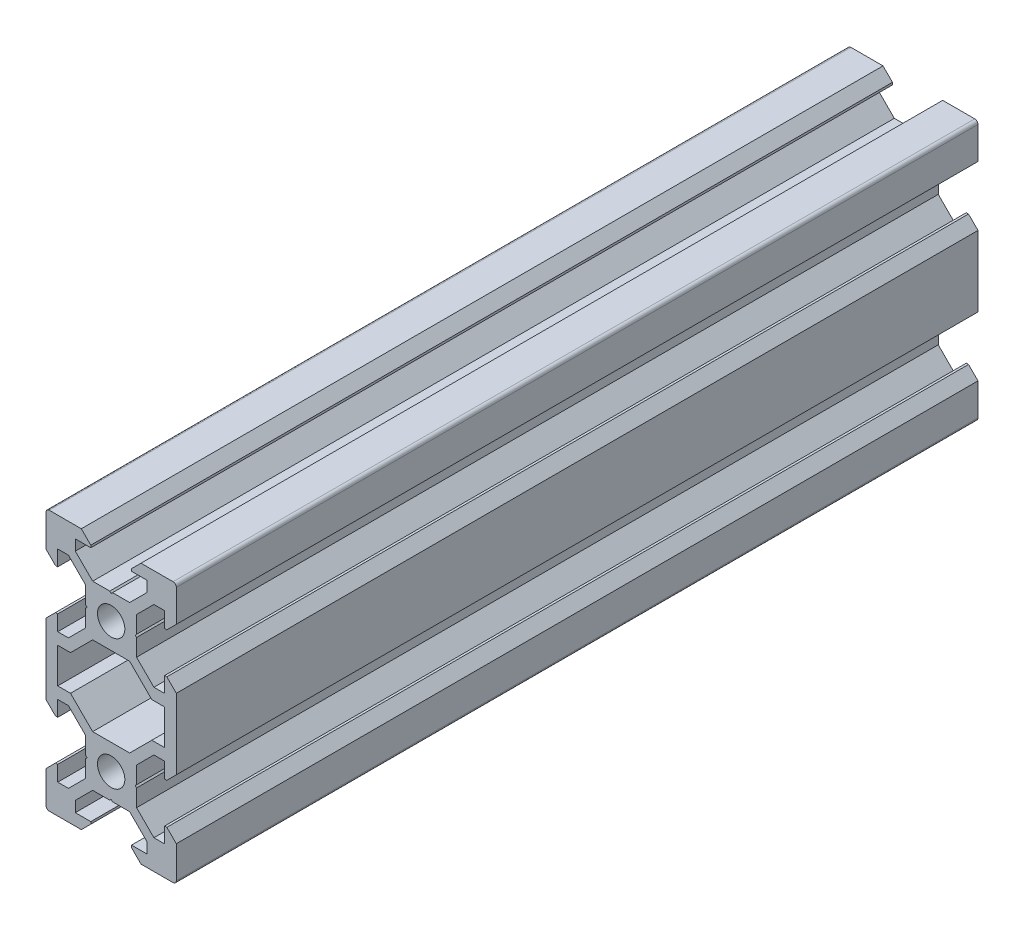
SolidWorks part; units mm, degrees
material "6061-T6 (SS)"
ref_plane "Front Plane" through (0, 0, 0) normal (0, 0, 1) x (1, 0, 0)
ref_plane "Top Plane" through (0, 0, 0) normal (0, 1, 0) x (1, 0, 0)
ref_plane "Right Plane" through (0, 0, 0) normal (1, 0, 0) x (0, 0, -1)
sketch "Sketch1" plane through (0, 0, 0) normal (0, 0, 1) x (1, 0, 0)
  line L0 (0, 0) -> (10, 0) construction
  line L1 (9.5, -20) -> (-9.5, -20)
  line L2 (10, -19.5) -> (10, 19.5)
  line L3 (9.5, 20) -> (-9.5, 20)
  line L4 (-10, -19.5) -> (-10, 19.5)
  line L5 (10, -20) -> (-10, 20) construction
  line L6 (10, 20) -> (-10, -20) construction
  circle A0 centre (0, 10) radius 2.1
  circle A1 centre (0, -10) radius 2.1
  arc A2 (-9.5, -20) -> (-10, -19.5) centre (-9.5, -19.5) cw
  arc A3 (9.5, -20) -> (10, -19.5) centre (9.5, -19.5) ccw
  arc A4 (10, 19.5) -> (9.5, 20) centre (9.5, 19.5) ccw
  arc A5 (-9.5, 20) -> (-10, 19.5) centre (-9.5, 19.5) ccw
  point P0 (0, 0)
  line B0 (0, 10) -> (0, 20) construction
  line B1 (0, 13.69) -> (-0.21, 13.9)
  line B2 (-0.21, 13.9) -> (-2.8393, 13.9)
  line B3 (-2.8393, 13.9) -> (-5.5, 16.5607)
  line B4 (-5.5, 16.5607) -> (-5.5, 18.2)
  line B5 (-5.5, 18.2) -> (-3.125, 18.2)
  line B6 (-3.125, 18.2) -> (-3.125, 18.545)
  line B7 (-3.125, 18.545) -> (-4.58, 20)
  line B8 (-4.58, 20) -> (4.58, 20)
  line B9 (0, 10) -> (-5.9132, 15.9132) construction
  line B10 (3.125, 18.545) -> (4.58, 20)
  line B11 (3.125, 18.2) -> (3.125, 18.545)
  line B12 (5.5, 18.2) -> (3.125, 18.2)
  line B13 (5.5, 16.5607) -> (5.5, 18.2)
  line B14 (2.8393, 13.9) -> (5.5, 16.5607)
  line B15 (0.21, 13.9) -> (2.8393, 13.9)
  line B16 (0, 13.69) -> (0.21, 13.9)
  line B17 (0, 10) -> (-10, 10) construction
  line B18 (-3.69, 10) -> (-3.9, 9.79)
  line B19 (-3.9, 9.79) -> (-3.9, 7.1607)
  line B20 (-3.9, 7.1607) -> (-6.5607, 4.5)
  line B21 (-6.5607, 4.5) -> (-8.2, 4.5)
  line B22 (-8.2, 4.5) -> (-8.2, 6.875)
  line B23 (-8.2, 6.875) -> (-8.545, 6.875)
  line B24 (-8.545, 6.875) -> (-10, 5.42)
  line B25 (-10, 5.42) -> (-10, 14.58)
  line B26 (0, 10) -> (-5.9132, 4.0868) construction
  line B27 (-8.545, 13.125) -> (-10, 14.58)
  line B28 (-8.2, 13.125) -> (-8.545, 13.125)
  line B29 (-8.2, 15.5) -> (-8.2, 13.125)
  line B30 (-6.5607, 15.5) -> (-8.2, 15.5)
  line B31 (-3.9, 12.8393) -> (-6.5607, 15.5)
  line B32 (-3.9, 10.21) -> (-3.9, 12.8393)
  line B33 (-3.69, 10) -> (-3.9, 10.21)
  line B34 (0, -10) -> (-10, -10) construction
  line B35 (-3.69, -10) -> (-3.9, -10.21)
  line B36 (-3.9, -10.21) -> (-3.9, -12.8393)
  line B37 (-3.9, -12.8393) -> (-6.5607, -15.5)
  line B38 (-6.5607, -15.5) -> (-8.2, -15.5)
  line B39 (-8.2, -15.5) -> (-8.2, -13.125)
  line B40 (-8.2, -13.125) -> (-8.545, -13.125)
  line B41 (-8.545, -13.125) -> (-10, -14.58)
  line B42 (-10, -14.58) -> (-10, -5.42)
  line B43 (0, -10) -> (-5.9132, -15.9132) construction
  line B44 (-8.545, -6.875) -> (-10, -5.42)
  line B45 (-8.2, -6.875) -> (-8.545, -6.875)
  line B46 (-8.2, -4.5) -> (-8.2, -6.875)
  line B47 (-6.5607, -4.5) -> (-8.2, -4.5)
  line B48 (-3.9, -7.1607) -> (-6.5607, -4.5)
  line B49 (-3.9, -9.79) -> (-3.9, -7.1607)
  line B50 (-3.69, -10) -> (-3.9, -9.79)
  line B51 (0, -10) -> (0, -20) construction
  line B52 (0, -13.69) -> (0.21, -13.9)
  line B53 (0.21, -13.9) -> (2.8393, -13.9)
  line B54 (2.8393, -13.9) -> (5.5, -16.5607)
  line B55 (5.5, -16.5607) -> (5.5, -18.2)
  line B56 (5.5, -18.2) -> (3.125, -18.2)
  line B57 (3.125, -18.2) -> (3.125, -18.545)
  line B58 (3.125, -18.545) -> (4.58, -20)
  line B59 (4.58, -20) -> (-4.58, -20)
  line B60 (0, -10) -> (5.9132, -15.9132) construction
  line B61 (-3.125, -18.545) -> (-4.58, -20)
  line B62 (-3.125, -18.2) -> (-3.125, -18.545)
  line B63 (-5.5, -18.2) -> (-3.125, -18.2)
  line B64 (-5.5, -16.5607) -> (-5.5, -18.2)
  line B65 (-2.8393, -13.9) -> (-5.5, -16.5607)
  line B66 (-0.21, -13.9) -> (-2.8393, -13.9)
  line B67 (0, -13.69) -> (-0.21, -13.9)
  line B68 (0, -10) -> (10, -10) construction
  line B69 (3.69, -10) -> (3.9, -9.79)
  line B70 (3.9, -9.79) -> (3.9, -7.1607)
  line B71 (3.9, -7.1607) -> (6.5607, -4.5)
  line B72 (6.5607, -4.5) -> (8.2, -4.5)
  line B73 (8.2, -4.5) -> (8.2, -6.875)
  line B74 (8.2, -6.875) -> (8.545, -6.875)
  line B75 (8.545, -6.875) -> (10, -5.42)
  line B76 (10, -5.42) -> (10, -14.58)
  line B77 (0, -10) -> (5.9132, -4.0868) construction
  line B78 (8.545, -13.125) -> (10, -14.58)
  line B79 (8.2, -13.125) -> (8.545, -13.125)
  line B80 (8.2, -15.5) -> (8.2, -13.125)
  line B81 (6.5607, -15.5) -> (8.2, -15.5)
  line B82 (3.9, -12.8393) -> (6.5607, -15.5)
  line B83 (3.9, -10.21) -> (3.9, -12.8393)
  line B84 (3.69, -10) -> (3.9, -10.21)
  line B85 (0, 10) -> (10, 10) construction
  line B86 (3.69, 10) -> (3.9, 10.21)
  line B87 (3.9, 10.21) -> (3.9, 12.8393)
  line B88 (3.9, 12.8393) -> (6.5607, 15.5)
  line B89 (6.5607, 15.5) -> (8.2, 15.5)
  line B90 (8.2, 15.5) -> (8.2, 13.125)
  line B91 (8.2, 13.125) -> (8.545, 13.125)
  line B92 (8.545, 13.125) -> (10, 14.58)
  line B93 (10, 14.58) -> (10, 5.42)
  line B94 (0, 10) -> (5.9132, 15.9132) construction
  line B95 (8.545, 6.875) -> (10, 5.42)
  line B96 (8.2, 6.875) -> (8.545, 6.875)
  line B97 (8.2, 4.5) -> (8.2, 6.875)
  line B98 (6.5607, 4.5) -> (8.2, 4.5)
  line B99 (3.9, 7.1607) -> (6.5607, 4.5)
  line B100 (3.9, 9.79) -> (3.9, 7.1607)
  line B101 (3.69, 10) -> (3.9, 9.79)
  line B102 (-8.2, -2.7) -> (-8.2, 2.7)
  line B103 (-8.2, 2.7) -> (-6.2393, 2.7)
  line B104 (-6.2393, 2.7) -> (-2.8393, 6.1)
  line B105 (-2.8393, 6.1) -> (2.8393, 6.1)
  line B106 (0, 6.1) -> (0, 0) construction
  line B107 (0, 0) -> (-8.2, 0) construction
  line B108 (6.2393, 2.7) -> (2.8393, 6.1)
  line B109 (8.2, 2.7) -> (6.2393, 2.7)
  line B110 (8.2, -2.7) -> (8.2, 2.7)
  line B111 (8.2, -2.7) -> (6.2393, -2.7)
  line B112 (6.2393, -2.7) -> (2.8393, -6.1)
  line B113 (-2.8393, -6.1) -> (2.8393, -6.1)
  line B114 (-6.2393, -2.7) -> (-2.8393, -6.1)
  line B115 (-8.2, -2.7) -> (-6.2393, -2.7)
  line B116 (0, 6.1) -> (0, 10) construction
  line B117 (0, 10) -> (-5.0927, 4.9073) construction
  dimension "D4" = 4.2
  dimension "D5" = 0.5
  dimension "D1" = 20
  dimension "D2" = 40
  dimension "D3" = 20
sketch_block_instance "V Slot 1-4"
sketch_block "V Slot 1" parameters "D1"=10, "D2"=11, "D3"=4.3, "D4"=1.8, "D5"=0.21, "D6"=45, "D7"=9.16, "D8"=1.5, "D9"=6.25
sketch_block_instance "V Slot 1-5"
sketch_block_instance "V Slot 1-6"
sketch_block_instance "V Slot 1-7"
sketch_block_instance "V Slot 1-8"
sketch_block_instance "V Slot 1-9"
sketch_block_instance "Center Cutout 1-1"
sketch_block "Center Cutout 1" parameters "D1"=5.4, "D2"=12.2, "D3"=8.2, "D4"=45, "D5"=10, "D6"=1.5
extrude "Boss-Extrude1" add sketch "Sketch1" along normal blind 123.05 contours B101 B86 B87 B88 B89 B90 B91 B92 L2 A4 L3 B10 B11 B12 B13 B14 B15 B16 B1 B2 B3 B4 B5 B6 B7 A5 L4 B27 B28 B29 B30 B31 B32 B33 B18 B19 B20 B21 B22 B23 B24 B44 B45 B46 B47 B48 B49 B50 B35
